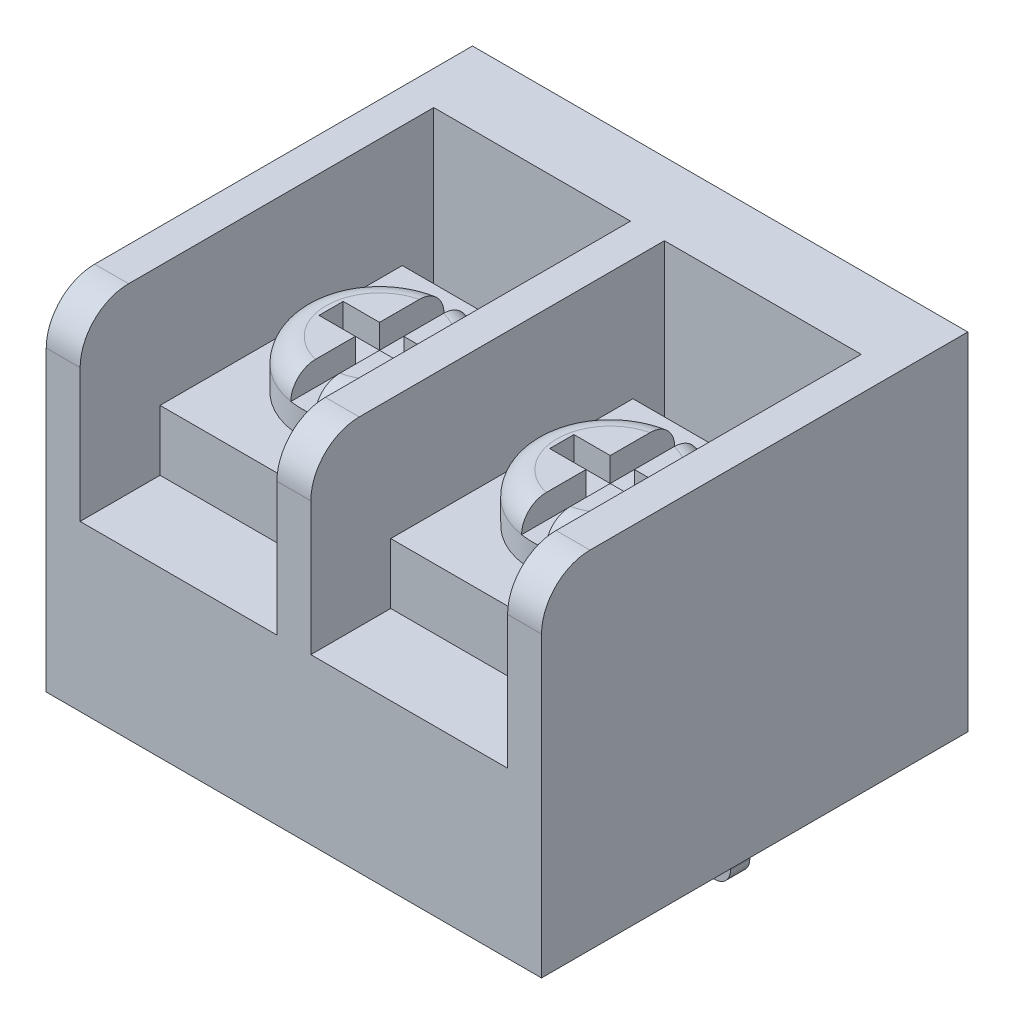
SolidWorks part; units mm, degrees
ref_plane "Front Plane" through (0, 0, 0) normal (0, 0, 1) x (1, 0, 0)
ref_plane "Top Plane" through (0, 0, 0) normal (0, 1, 0) x (1, 0, 0)
ref_plane "Right Plane" through (0, 0, 0) normal (1, 0, 0) x (0, 0, -1)
sketch "Sketch1" plane through (0, 0, 0) normal (0, 1, 0) x (1, 0, 0)
  line L1 (-10.225, 8.8) -> (10.225, 8.8)
  line L2 (-10.225, 8.8) -> (-10.225, -8.8)
  line L3 (-10.225, -8.8) -> (10.225, -8.8)
  line L4 (10.225, 8.8) -> (10.225, -8.8)
  line L5 (-10.225, 8.8) -> (10.225, -8.8) construction
  line L6 (-10.225, -8.8) -> (10.225, 8.8) construction
  point P0 (0, 0)
  dimension "D1" = 20.45
  dimension "D2" = 17.6
extrude "Boss-Extrude1" add sketch "Sketch1" along normal blind 14.3
fillet "Fillet1" radius 2 1 edges at (0, 14.3, 8.8)
sketch "Sketch2" plane through (0, 14.3, 0) normal (0, 1, 0) x (1, 0, 0)
  line L0 (-10.225, -8.8) -> (10.225, -8.8) construction
  line L1 (-8.825, 5.8) -> (-0.7, 5.8)
  line L2 (-8.825, 5.8) -> (-8.825, -8.8)
  line L3 (-8.825, -8.8) -> (-0.7, -8.8)
  line L4 (-0.7, 5.8) -> (-0.7, -8.8)
  line L5 (10.225, 8.8) -> (-10.225, 8.8) construction
  line L6 (0.7, 5.8) -> (8.825, 5.8)
  line L7 (0.7, 5.8) -> (0.7, -8.8)
  line L8 (0.7, -8.8) -> (8.825, -8.8)
  line L9 (8.825, 5.8) -> (8.825, -8.8)
  line L10 (-10.225, 8.8) -> (-10.225, -6.8) construction
  line L11 (10.225, -6.8) -> (10.225, 8.8) construction
  line L12 (-0.7, 0) -> (0.7, 0) construction
  point P18 (0, 0)
  dimension "D1" = 3
  dimension "D2" = 1.4
  dimension "D3" = 1.4
  dimension "D4" = 1.4
extrude "Cut-Extrude1" cut sketch "Sketch2" against normal blind 7.5
sketch "Sketch3" plane through (0, 0, 0) normal (0, -1, 0) x (1, 0, 0)
  line L0 (-4.075, -3.8) -> (4.075, -3.8) construction
  line L1 (-5.425, -3.8) -> (-4.075, -3.8)
  line L2 (-5.425, -3.8) -> (-5.425, -4.6)
  line L3 (-5.425, -4.6) -> (-4.075, -4.6)
  line L4 (-4.075, -3.8) -> (-4.075, -4.6)
  line L5 (4.075, -3.8) -> (5.425, -3.8)
  line L6 (4.075, -3.8) -> (4.075, -4.6)
  line L7 (4.075, -4.6) -> (5.425, -4.6)
  line L8 (5.425, -3.8) -> (5.425, -4.6)
  line L9 (10.225, -8.8) -> (-10.225, -8.8) construction
  point P8 (0, -3.8)
  point P9 (-4.75, -4.6)
  point P11 (4.75, -4.6)
  dimension "D1" = 0.8
  dimension "D2" = 1.35
  dimension "D3" = 9.5
  dimension "D4" = 4.2
extrude "Boss-Extrude2" add sketch "Sketch3" along normal blind 5.5 separate body
fillet "Fillet3" radius 0.65 2 edges at (5.425, -5.5, -4.2) (4.075, -5.5, -4.2)
fillet "Fillet4" radius 0.65 2 edges at (-5.425, -5.5, -4.2) (-4.075, -5.5, -4.2)
sketch "Sketch4" plane through (0, 6.8, 0) normal (0, 1, 0) x (1, 0, 0)
  line L0 (-8.825, 5.8) -> (-8.825, -8.8) construction
  line L1 (-8.825, 4.5) -> (-0.7, 4.5)
  line L2 (-8.825, 4.5) -> (-8.825, -5.5)
  line L3 (-8.825, -5.5) -> (-0.7, -5.5)
  line L4 (-0.7, 4.5) -> (-0.7, -5.5)
  line L5 (-0.7, -8.8) -> (-0.7, 5.8) construction
  line L6 (-8.825, -8.8) -> (-0.7, -8.8) construction
  line L7 (0.7, 5.8) -> (0.7, -8.8) construction
  line L8 (0.7, 4.5) -> (8.825, 4.5)
  line L9 (0.7, 4.5) -> (0.7, -5.5)
  line L10 (0.7, -5.5) -> (8.825, -5.5)
  line L11 (8.825, 4.5) -> (8.825, -5.5)
  line L12 (8.825, -8.8) -> (8.825, 5.8) construction
  dimension "D1" = 3.3
  dimension "D2" = 10
extrude "Boss-Extrude3" add sketch "Sketch4" along normal blind 2.5 separate body
sketch "Sketch5" plane through (0, 9.3, 0) normal (0, 1, 0) x (1, 0, 0)
  line L0 (-0.7, 4.5) -> (-8.825, 4.5) construction
  line L1 (8.825, 4.5) -> (0.7, 4.5) construction
  line L2 (0.7, 4.5) -> (0.7, -5.5) construction
  line L3 (-8.825, 4.5) -> (-8.825, -5.5) construction
  circle A0 centre (-4.7625, -0.5) radius 3.2
  circle A1 centre (4.7625, -0.5) radius 3.2
  point P6 (-4.7625, 4.5)
  point P9 (4.7625, 4.5)
  point P12 (0.7, -0.5)
  point P15 (-8.825, -0.5)
  dimension "D1" = 6.4
extrude "Boss-Extrude4" add sketch "Sketch5" along normal blind 2
sketch "Sketch6" plane through (0, 11.3, 0) normal (0, 1, 0) x (1, 0, 0)
  line L0 (-5.2625, 2.7) -> (-5.2625, 0)
  line L1 (-5.2625, 0) -> (-6.7625, 0)
  line L2 (-6.7625, 0) -> (-6.7625, -1)
  line L3 (-6.7625, -1) -> (-5.2625, -1)
  line L4 (-5.2625, -1) -> (-5.2625, -3.7)
  line L5 (-5.2625, -3.7) -> (-4.2625, -3.7)
  line L6 (-4.2625, -3.7) -> (-4.2625, -1)
  line L7 (-4.2625, -1) -> (-2.7625, -1)
  line L8 (-2.7625, -1) -> (-2.7625, 0)
  line L9 (-2.7625, 0) -> (-4.2625, 0)
  line L10 (-4.2625, 0) -> (-4.2625, 2.7)
  line L11 (-4.2625, 2.7) -> (-5.2625, 2.7)
  line L12 (0, 7.1419) -> (0, -12.2187) construction
  line L13 (4.2625, 0) -> (4.2625, 2.7)
  line L14 (2.7625, 0) -> (4.2625, 0)
  line L15 (2.7625, -1) -> (2.7625, 0)
  line L16 (4.2625, -1) -> (2.7625, -1)
  line L17 (4.2625, -3.7) -> (4.2625, -1)
  line L18 (5.2625, -3.7) -> (4.2625, -3.7)
  line L19 (5.2625, -1) -> (5.2625, -3.7)
  line L20 (6.7625, -1) -> (5.2625, -1)
  line L21 (6.7625, 0) -> (6.7625, -1)
  line L22 (5.2625, 0) -> (6.7625, 0)
  line L23 (5.2625, 2.7) -> (5.2625, 0)
  line L24 (4.2625, 2.7) -> (5.2625, 2.7)
  circle A0 centre (-4.7625, -0.5) radius 3.2 construction
  point P11 (-4.7625, -0.5)
  point P14 (-4.7625, 2.7)
  point P16 (-6.7625, -0.5)
  dimension "D1" = 4
extrude "Cut-Extrude2" cut sketch "Sketch6" against normal blind 1
fillet "Fillet5" radius 1 2 edges at (-1.5625, 11.3, 0.5) (-7.9625, 11.3, 0.5)
fillet "Fillet6" radius 1 2 edges at (7.9625, 11.3, 0.5) (1.5625, 11.3, 0.5)
